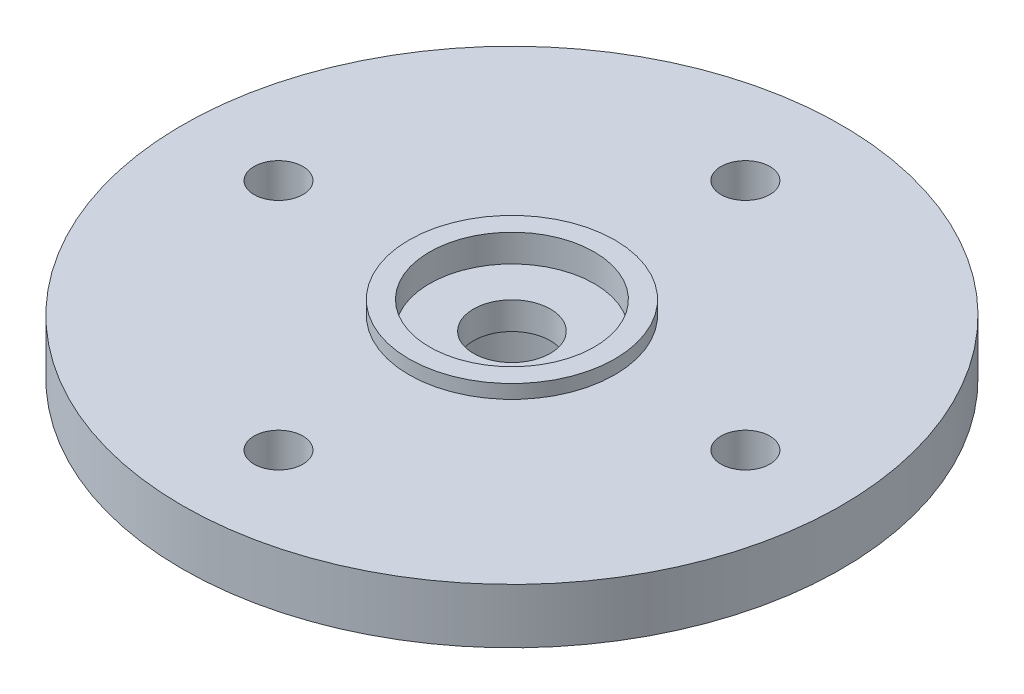
SolidWorks part; units mm, degrees
material "1345 Alloy"
ref_plane "Front Plane" through (0, 0, 0) normal (0, 0, 1) x (1, 0, 0)
ref_plane "Top Plane" through (0, 0, 0) normal (0, 1, 0) x (1, 0, 0)
ref_plane "Right Plane" through (0, 0, 0) normal (1, 0, 0) x (0, 0, -1)
ref_plane "Plane1" through (0, 0, 0) normal (0, 0, -1) x (-1, 0, 0)
sketch "Sketch1" plane through (0, 0, 0) normal (0, 0, -1) x (-1, 0, 0)
  line L0 (32.069, 68.0571) -> (44.069, 68.0571)
  line L1 (44.069, 68.0571) -> (44.069, 70.0571)
  line L2 (44.069, 70.0571) -> (32.069, 70.0571)
  line L3 (32.069, 70.0571) -> (32.069, 68.0571)
  line L4 (44.069, 68.0571) -> (44.069, 70.0571) construction
revolve "Revolve1" add sketch "Sketch1" angle 360 about L4
sketch "Sketch2" plane through (0, 68.0571, 0) normal (0, -1, 0) x (1, 0, 0)
  circle A0 centre (-44.069, 0) radius 4.5
extrude "Boss-Extrude1" add sketch "Sketch2" along normal blind 2.5
sketch "Sketch3" plane through (0, 70.0571, 0) normal (0, 1, 0) x (-1, 0, 0)
  circle A0 centre (44.069, 0) radius 3.75
extrude "Boss-Extrude2" add sketch "Sketch3" along normal blind 0.5
sketch "Sketch4" plane through (0, 0, 0) normal (0, 0, 1) x (1, 0, 0)
  line L0 (-41.069, 70.5571) -> (-44.069, 70.5571)
  line L1 (-44.069, 70.5571) -> (-44.069, 65.5571)
  line L2 (-44.069, 65.5571) -> (-41.069, 65.5571)
  line L3 (-41.069, 65.5571) -> (-41.069, 68.5571)
  line L4 (-41.069, 68.5571) -> (-42.669, 68.5571)
  line L5 (-42.669, 68.5571) -> (-42.669, 69.5571)
  line L6 (-42.669, 69.5571) -> (-41.069, 69.5571)
  line L7 (-41.069, 69.5571) -> (-41.069, 70.5571)
  line L8 (-44.069, 70.5571) -> (-44.069, 65.5571) construction
revolve "Cut-Revolve1" cut sketch "Sketch4" angle 360 about L8
hole_wizard "M1.6 Clearance Hole1" positions "Sketch6" profile "Sketch5" hole size "M1.6" standard "ANSI Metric"
sketch "Sketch6" plane through (0, 68.0571, 0) normal (0, -1, 0) x (-1, 0, 0)
  point P0 (44.069, 8.5)
  point P1 (52.569, 0)
  point P2 (35.569, 0)
  point P3 (44.069, -8.5)
sketch "Sketch5" plane through (-44.069, 68.0571, -8.5) normal (1, 0, 0) x (0, 0, -1)
  line L0 (0, 0) -> (0, 2.5)
  line L1 (0, 2.5) -> (0.889, 2.5)
  line L2 (0.889, 2.5) -> (0.889, 0)
  line L5 (0.889, 0) -> (0, 0)
  line L11 (0, -6.35) -> (0, 107.95) construction
  dimension "Thru Hole Dia." = 1.778
  dimension "Thru Hole Depth" = 2.5
